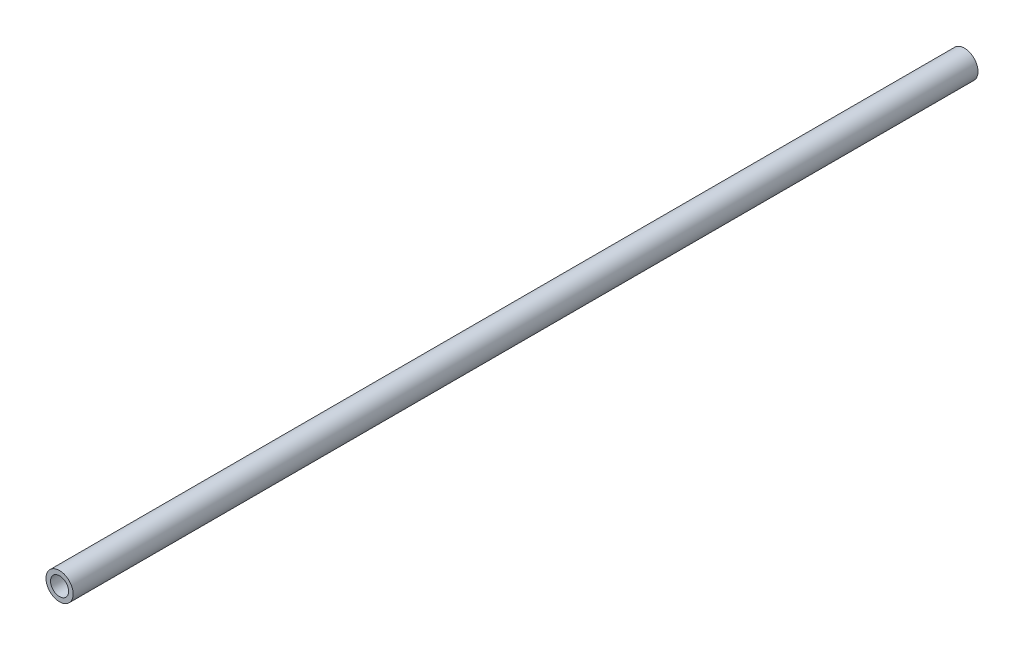
SolidWorks part; units mm, degrees
material "PVC Rigid"
ref_plane "Front Plane" through (0, 0, 0) normal (0, 0, 1) x (1, 0, 0)
ref_plane "Top Plane" through (0, 0, 0) normal (0, 1, 0) x (1, 0, 0)
ref_plane "Right Plane" through (0, 0, 0) normal (1, 0, 0) x (0, 0, -1)
sketch "Sketch1" plane through (0, 0, 0) normal (0, 0, 1) x (1, 0, 0)
  circle A0 centre (0, 0) radius 7.62
  circle A2 centre (0, 0) radius 5.08
  dimension "D1" = 15.24
  dimension "D2" = 10.16
extrude "Boss-Extrude1" add sketch "Sketch1" along normal blind 508
